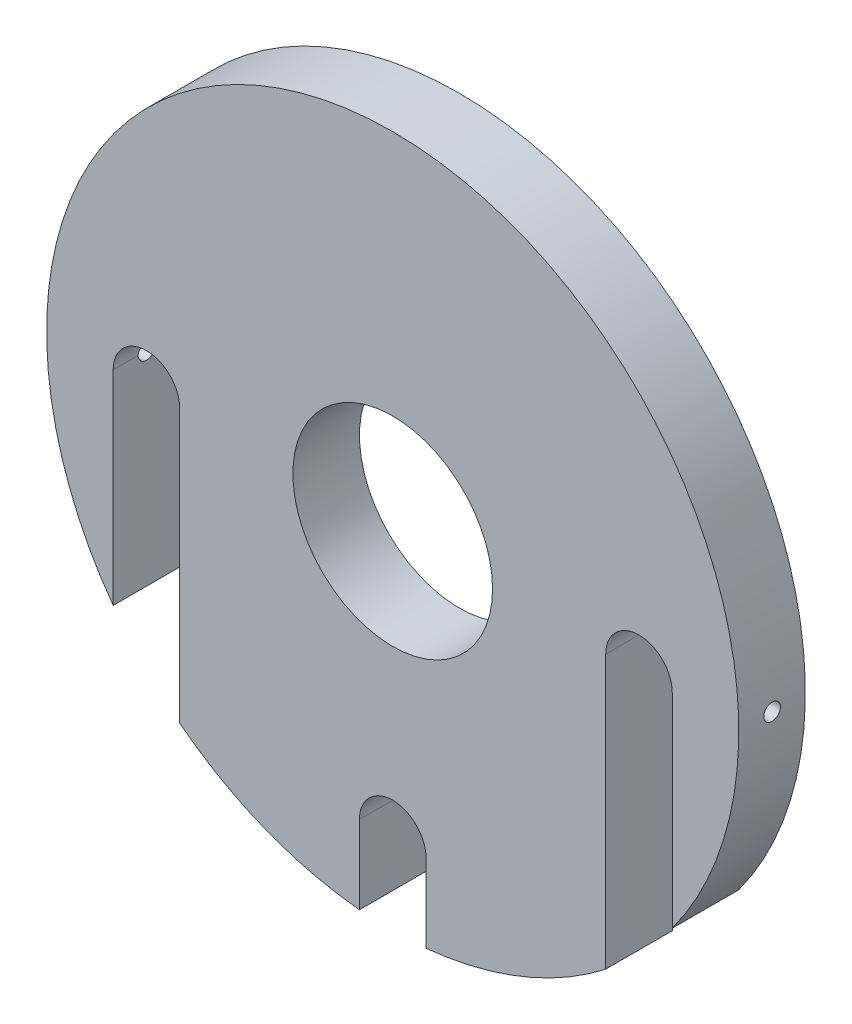
SolidWorks part; units mm, degrees
material "Malleable Cast Iron"
ref_plane "Front Plane" through (0, 0, 0) normal (0, 0, 1) x (1, 0, 0)
ref_plane "Top Plane" through (0, 0, 0) normal (0, 1, 0) x (1, 0, 0)
ref_plane "Right Plane" through (0, 0, 0) normal (1, 0, 0) x (0, 0, -1)
sketch "Sketch1" plane through (0, 0, 0) normal (0, 0, 1) x (1, 0, 0)
  circle A0 centre (0, 0) radius 52
  dimension "D1" = 104
extrude "Boss-Extrude1" add sketch "Sketch1" along normal blind 10
sketch "Sketch2" plane through (0, 0, 10) normal (0, 0, 1) x (1, 0, 0)
  line L0 (0, 0) -> (0, -16.5156) construction
  line L2 (32, 0) -> (32, -45)
  line L3 (32, -45) -> (42, -45)
  line L4 (42, 0) -> (42, -45)
  line L6 (-5, -40) -> (-5, -55)
  line L7 (-5, -55) -> (5, -55)
  line L8 (5, -40) -> (5, -55)
  line L9 (-32, -45) -> (-42, -45)
  line L10 (-42, 0) -> (-42, -45)
  line L12 (-32, 0) -> (-32, -45)
  arc A1 (32, 0) -> (42, 0) centre (37, 0) cw
  arc A2 (-32, 0) -> (-42, 0) centre (-37, 0) ccw
  arc A3 (5, -40) -> (-5, -40) centre (0, -40) ccw
  dimension "D9" = 5
  dimension "D3" = 5
  dimension "D2" = 5
extrude "Cut-Extrude1" cut sketch "Sketch2" against normal blind 10
sketch "Sketch3" plane through (0, 0, 10) normal (0, 0, 1) x (1, 0, 0)
  circle A0 centre (0, 0) radius 15
  dimension "D1" = 30
extrude "Cut-Extrude2" cut sketch "Sketch3" against normal blind 10
ref_plane "Plane2" through (52, 0, 0) normal (1, 0, 0) x (0, 0, -1)
hole_wizard "M3 Tapped Hole3" positions "Sketch10" profile "Sketch11" tap size "M3" standard "ISO"
sketch "Sketch10" plane through (52, 0, 0) normal (1, 0, 0) x (0, 0, -1)
  point P0 (-5, 0)
  dimension "D1" = 5
sketch "Sketch11" plane through (52, 0, 5) normal (0, 1, 0) x (0, 0, -1)
  line L0 (0, 0) -> (0, 37)
  line L1 (0, 37) -> (1.25, 37)
  line L2 (1.25, 37) -> (1.25, 0)
  line L5 (1.25, 0) -> (0, 0)
  line L11 (0, -6.35) -> (0, 107.95) construction
  dimension "Thru Tap Drill Dia." = 2.5
  dimension "Thru Tap Drill Depth" = 37
cosmetic thread "Hole Thread3" parameters "D2"=3
mirror "Mirror1" about plane through (0, 0, 0) normal (1, 0, 0) of "M3 Tapped Hole3"
